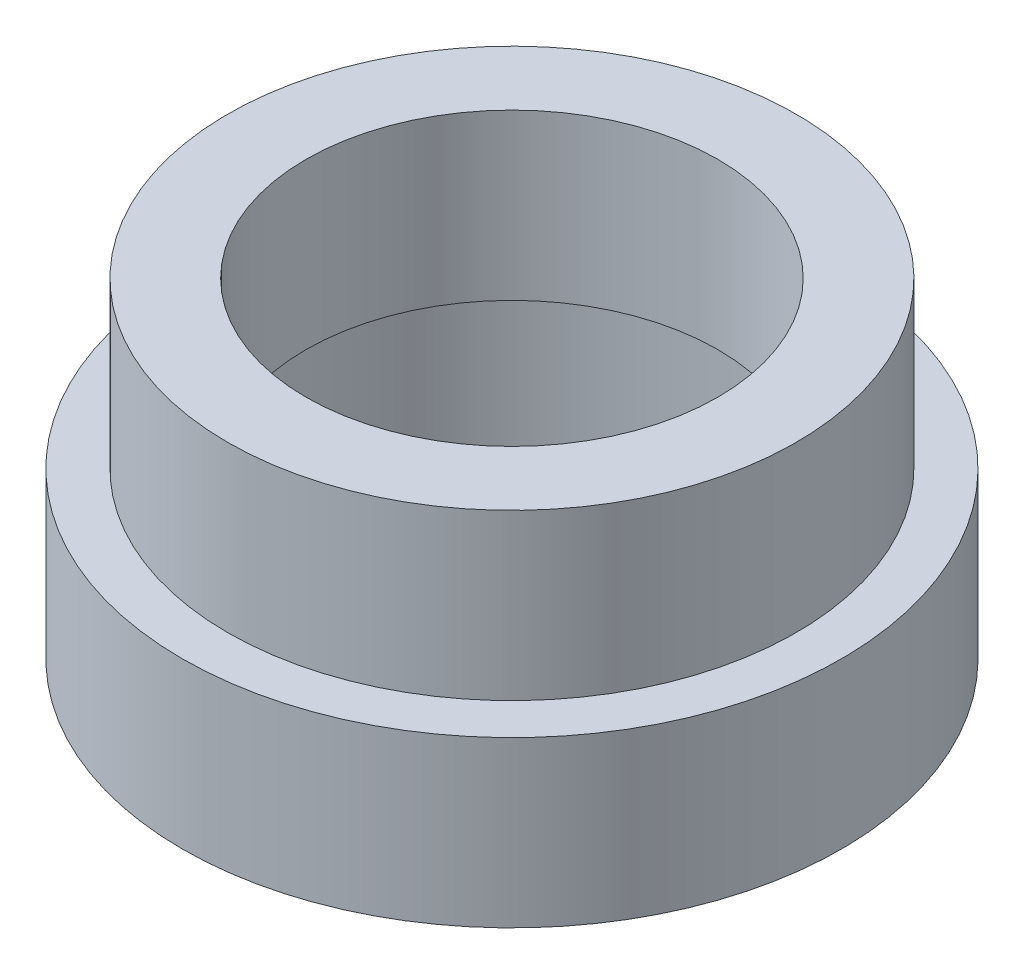
SolidWorks part; units mm, degrees
ref_plane "Front Plane" through (0, 0, 0) normal (0, 0, 1) x (1, 0, 0)
ref_plane "Top Plane" through (0, 0, 0) normal (0, 1, 0) x (1, 0, 0)
ref_plane "Right Plane" through (0, 0, 0) normal (1, 0, 0) x (0, 0, -1)
sketch "Sketch2" plane through (0, 0, 0) normal (0, 1, 0) x (1, 0, 0)
  circle A0 centre (0, 0) radius 17.25
  circle A1 centre (0, 0) radius 15
  dimension "D1" = 30
  dimension "D2" = 34.5
extrude "Boss-Extrude4" add sketch "Sketch2" along normal blind 20
sketch "Sketch4" plane through (0, 0, 0) normal (0, 1, 0) x (1, 0, 0)
  circle A0 centre (0, 0) radius 20
  circle A1 centre (0, 0) radius 15
  dimension "D1" = 30
  dimension "D2" = 40
extrude "Boss-Extrude6" add sketch "Sketch4" along normal blind 10
sketch "Sketch5" plane through (0, 0, 0) normal (0, 1, 0) x (1, 0, 0)
  circle A0 centre (0, 0) radius 15
  circle A1 centre (0, 0) radius 12.5
  dimension "D1" = 30
  dimension "D2" = 25
extrude "Boss-Extrude7" add sketch "Sketch5" along normal blind 10 from offset 10
